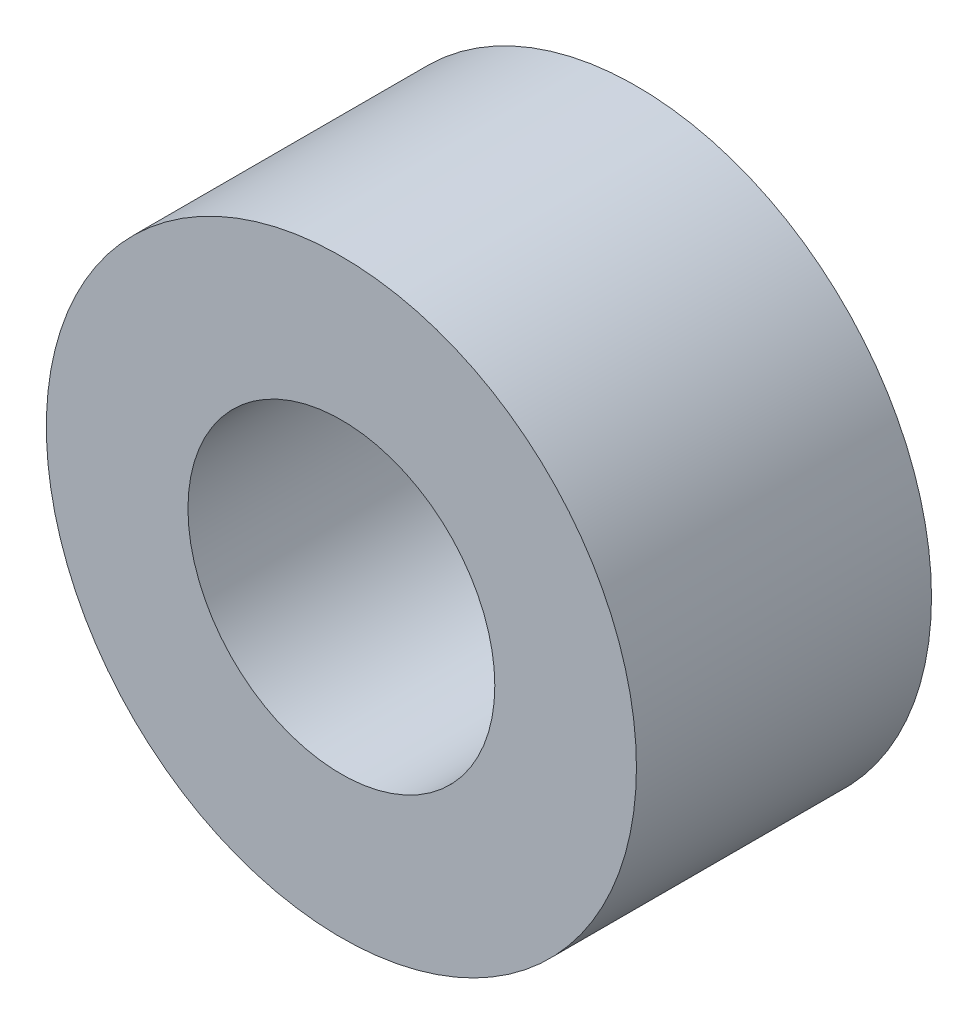
SolidWorks part; units mm, degrees
ref_plane "Front Plane" through (0, 0, 0) normal (0, 0, 1) x (1, 0, 0)
ref_plane "Top Plane" through (0, 0, 0) normal (0, 1, 0) x (1, 0, 0)
ref_plane "Right Plane" through (0, 0, 0) normal (1, 0, 0) x (0, 0, -1)
sketch "Sketch1" plane through (0, 0, 0) normal (0, 0, 1) x (1, 0, 0)
  circle A0 centre (0, 0) radius 6.35
  dimension "D1" = 12.7
extrude "Boss-Extrude1" add sketch "Sketch1" along normal blind 6.35
sketch "Sketch2" plane through (0, 0, 6.35) normal (0, 0, 1) x (1, 0, 0)
  circle A0 centre (0, 0) radius 3.302
  dimension "D1" = 6.604
extrude "Cut-Extrude1" cut sketch "Sketch2" against normal through all
